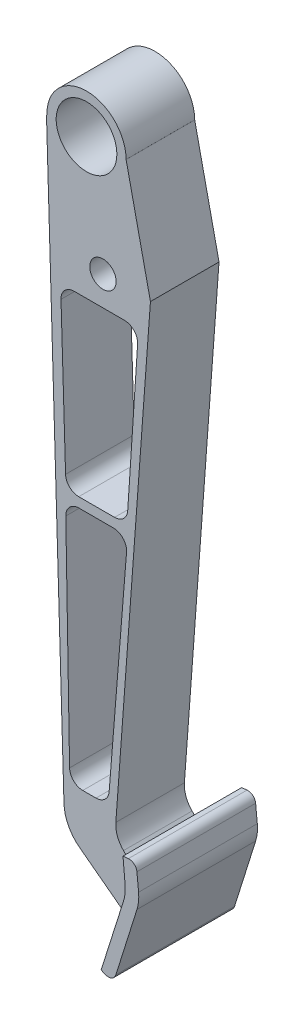
SolidWorks part; units mm, degrees
material "Cast Alloy Steel"
ref_plane "Front Plane" through (0, 0, 0) normal (0, 0, 1) x (1, 0, 0)
ref_plane "Top Plane" through (0, 0, 0) normal (0, 1, 0) x (1, 0, 0)
ref_plane "Right Plane" through (0, 0, 0) normal (1, 0, 0) x (0, 0, -1)
sketch "Sketch1" plane through (0, 0, 0) normal (0, 0, 1) x (1, 0, 0)
  line L2 (-0.7507, -9.9312) -> (-13.8715, -187.4566)
  line L3 (-27.5658, -202.6012) -> (-6.8269, -218.2622)
  line L4 (-10.9698, -195.2647) -> (-2.2968, -203.9377)
  line L5 (-6.8269, -218.2622) -> (-2.2968, -203.9377)
  line L6 (-9.9771, 32.0757) -> (-9.9782, 32.0757)
  line L7 (-9.9782, 32.0757) -> (-9.9767, 32.0752)
  line L8 (-39.976, 32.073) -> (-40.144, 31.2674)
  line L9 (-40.144, 31.2674) -> (-33.5201, -191.0651)
  line L10 (-9.9767, 32.0752) -> (-9.9782, 32.0757)
  line L11 (-9.9767, 32.0752) -> (-9.9714, 32.0634)
  line L12 (-9.9714, 32.0634) -> (-0.7507, -9.9312)
  arc A0 (-9.9771, 32.0753) -> (-39.9771, 32.0676) centre (-24.9771, 32.0757) ccw
  circle A1 centre (-18.7507, -9.9243) radius 5
  arc A2 (-33.5201, -191.0651) -> (-27.5658, -202.6012) centre (-18.5264, -190.6308) ccw
  arc A3 (-13.8715, -187.4566) -> (-10.9698, -195.2647) centre (-3.8987, -188.1937) ccw
  point P12 (-33.3117, -198.2622)
  dimension "D1" = 30
  dimension "D3" = 10
  dimension "D6" = 15
  dimension "D7" = 10
  dimension "D4" = 42
  dimension "D5" = 20
  dimension "D9" = 18
extrude "Boss-Extrude2" add sketch "Sketch1" along normal blind 26
sketch "Sketch9" plane through (0, 0, 0) normal (0, 0, 1) x (1, 0, 0)
  circle A1 centre (-24.9771, 32.0757) radius 11.5
  dimension "D1" = 23
extrude "Cut-Extrude7" cut sketch "Sketch9" along normal blind 26
sketch "Sketch10" plane through (0, 0, 0) normal (0, 0, 1) x (1, 0, 0)
  line L0 (-29.6545, -21.0023) -> (-10.6028, -21.0023)
  line L1 (-5.6138, -26.3332) -> (-9.366, -82.9049)
  line L2 (-14.355, -87.574) -> (-27.9227, -87.574)
  line L3 (-34.6522, -26.1552) -> (-32.9204, -82.727)
  line L4 (-14.7849, -91.271) -> (-27.8323, -91.271)
  line L5 (-32.8315, -96.3583) -> (-31.3996, -178.3298)
  line L6 (-26.4004, -183.2425) -> (-21.3869, -183.2425)
  line L7 (-16.4031, -178.6439) -> (-9.801, -96.6724)
  arc A0 (-14.355, -87.574) -> (-9.366, -82.9049) centre (-14.355, -82.574) ccw
  arc A1 (-27.9227, -87.574) -> (-32.9204, -82.727) centre (-27.9227, -82.574) cw
  arc A2 (-29.6545, -21.0023) -> (-34.6522, -26.1552) centre (-29.6545, -26.0023) ccw
  arc A3 (-10.6028, -21.0023) -> (-5.6138, -26.3332) centre (-10.6028, -26.0023) cw
  arc A4 (-9.801, -96.6724) -> (-14.7849, -91.271) centre (-14.7849, -96.271) ccw
  arc A5 (-27.8323, -91.271) -> (-32.8315, -96.3583) centre (-27.8323, -96.271) ccw
  arc A6 (-31.3996, -178.3298) -> (-26.4004, -183.2425) centre (-26.4004, -178.2425) ccw
  arc A7 (-21.3869, -183.2425) -> (-16.4031, -178.6439) centre (-21.3869, -178.2425) ccw
  dimension "D1" = 5
  dimension "D2" = 5
extrude "Cut-Extrude8" cut sketch "Sketch10" along normal blind 57
sketch "Sketch11" plane through (0, 0, 0) normal (0, 0, 1) x (1, 0, 0)
  line L0 (-2.2968, -203.9377) -> (-6.8269, -218.2622)
  line L1 (-6.8269, -218.2622) -> (-10.4452, -229.7037)
  line L2 (-2.2968, -203.9377) -> (-1.9953, -202.9844)
  line L3 (-1.356, -197.1355) -> (-2.1516, -188.1709)
  line L4 (-2.1516, -188.1709) -> (-0.129, -187.9913)
  line L5 (-10.4452, -229.7037) -> (-8.9163, -230.3673)
  line L6 (3.1216, -190.6838) -> (3.7548, -197.0741)
  line L7 (3.1386, -203.0477) -> (-4.8597, -228.5142)
  arc A0 (3.7548, -197.0741) -> (3.1386, -203.0477) centre (-11.1721, -198.5531) cw
  arc A1 (-1.9953, -202.9844) -> (-1.356, -197.1355) centre (-16.2972, -198.4615) ccw
  arc A2 (-4.8597, -228.5142) -> (-8.9163, -230.3673) centre (-7.7219, -227.6153) cw
  arc A3 (3.1216, -190.6838) -> (-0.129, -187.9913) centre (0.1362, -190.9796) ccw
  point P14 (-1.0907, -200.1239)
  point P17 (-5.8585, -231.6944)
  point P20 (2.8289, -187.7288)
  dimension "D6" = 15
  dimension "D7" = 3
  dimension "D1" = 12
  dimension "D2" = 4
  dimension "D3" = 12
  dimension "D4" = 5
  dimension "D5" = 5
extrude "Boss-Extrude5" add sketch "Sketch11" along normal blind 35 and the other way blind 10
